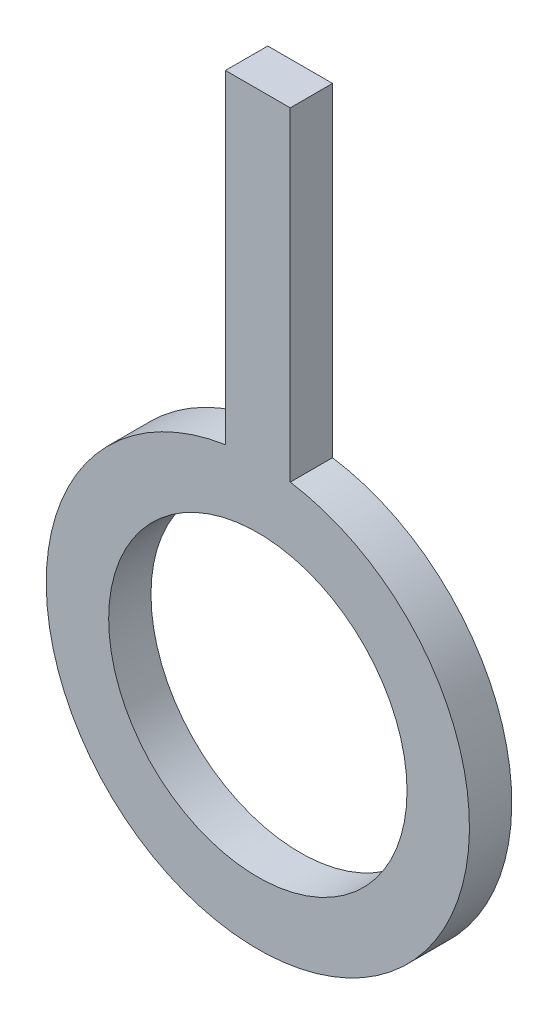
SolidWorks part; units mm, degrees
ref_plane "Front Plane" through (0, 0, 0) normal (0, 0, 1) x (1, 0, 0)
ref_plane "Top Plane" through (0, 0, 0) normal (0, 1, 0) x (1, 0, 0)
ref_plane "Right Plane" through (0, 0, 0) normal (1, 0, 0) x (0, 0, -1)
sketch "Sketch1" plane through (0, 0, 0) normal (0, 0, 1) x (1, 0, 0)
  line L4 (-1.5309, 25.1997) -> (1.5309, 25.1997)
  line L5 (-1.5309, 25.1997) -> (-1.5309, 9.8821)
  line L6 (1.5309, 25.1997) -> (1.5309, 9.8821)
  circle A1 centre (0, 0) radius 7.05
  arc A4 (-1.5309, 9.8821) -> (1.5309, 9.8821) centre (0, 0) ccw
  point P8 (0, 25.1997)
  dimension "D1" = 10
  dimension "D2" = 14.1
extrude "Boss-Extrude1" add sketch "Sketch1" along normal blind 2
